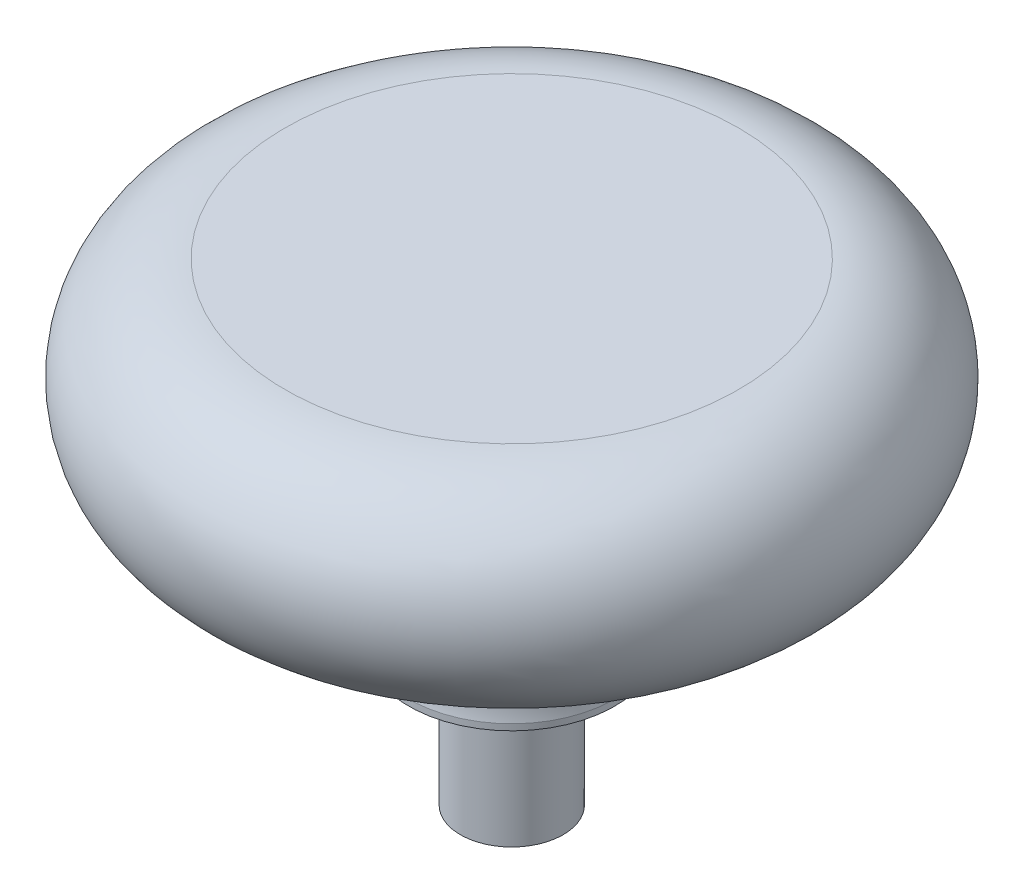
SolidWorks part; units mm, degrees
ref_plane "Front Plane" through (0, 0, 0) normal (0, 0, 1) x (1, 0, 0)
ref_plane "Top Plane" through (0, 0, 0) normal (0, 1, 0) x (1, 0, 0)
ref_plane "Right Plane" through (0, 0, 0) normal (1, 0, 0) x (0, 0, -1)
sketch "Sketch1" plane through (0, 0, 0) normal (0, 0, 1) x (1, 0, 0)
  line L0 (0, 0) -> (2.38, 0)
  line L1 (2.38, 0) -> (2.38, 6.35)
  line L2 (2.38, 6.35) -> (4.77, 6.35)
  line L3 (4.77, 6.35) -> (4.77, 6.6352)
  line L4 (10.5, 12.3744) -> (10.5, 17.1414) construction
  line L5 (0, 0) -> (0, 21.9114)
  line L6 (0, 21.9114) -> (10.5, 21.9114)
  arc A0 (9.4, 12.5) -> (4.77, 6.6352) centre (9.4127, 7.73) ccw
  arc A1 (9.4, 12.5) -> (10.5, 21.9114) centre (10.5, 17.1414) ccw
  point P6 (0, 0)
  point P9 (0, 0)
  point P14 (0, 0)
  point P15 (0, 0)
  point P16 (0, 0)
  point P17 (0, 0)
  point P18 (0, 0)
  point P19 (0, 0)
  dimension "D6" = 4.77
  dimension "D7" = 4.77
  dimension "D1" = 2.38
  dimension "D2" = 6.35
  dimension "D3" = 2.39
  dimension "D4" = 4.767
  dimension "D5" = 10.5
revolve "Revolve1" add sketch "Sketch1" angle 360 about L5
